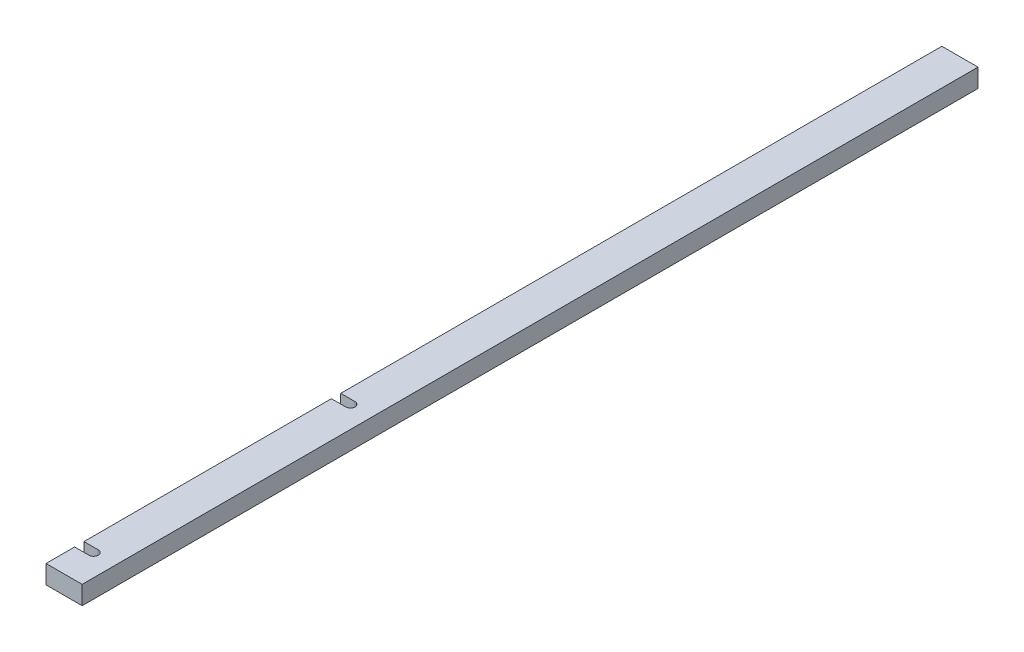
SolidWorks part; units mm, degrees
ref_plane "Front Plane" through (0, 0, 0) normal (0, 0, 1) x (1, 0, 0)
ref_plane "Top Plane" through (0, 0, 0) normal (0, 1, 0) x (1, 0, 0)
ref_plane "Right Plane" through (0, 0, 0) normal (1, 0, 0) x (0, 0, -1)
sketch "Sketch1" plane through (0, 0, 0) normal (0, 0, 1) x (1, 0, 0)
  line L1 (-26.0809, 10.1006) -> (11.9191, 10.1006)
  line L2 (-26.0809, 10.1006) -> (-26.0809, -9.3994)
  line L3 (-26.0809, -9.3994) -> (11.9191, -9.3994)
  line L4 (11.9191, 10.1006) -> (11.9191, -9.3994)
  dimension "D1" = 19.5
  dimension "D2" = 38
extrude "Boss-Extrude1" add sketch "Sketch1" along normal blind 942
sketch "Sketch2" plane through (0, -9.3994, 0) normal (0, -1, 0) x (1, 0, 0)
  line L0 (-11.0809, 911.9) -> (-32.6439, 911.9)
  line L1 (-32.6439, 911.9) -> (-32.6439, 902.1)
  line L2 (-32.6439, 902.1) -> (-11.0809, 902.1)
  line L3 (-11.0809, 641.9) -> (-28.707, 641.9)
  line L4 (-28.707, 641.9) -> (-28.707, 632.1)
  line L5 (-28.707, 632.1) -> (-11.0809, 632.1)
  arc A0 (-11.0809, 902.1) -> (-11.0809, 911.9) centre (-11.0809, 907) ccw
  arc A1 (-11.0809, 632.1) -> (-11.0809, 641.9) centre (-11.0809, 637) ccw
  dimension "D1" = 4.9
extrude "Cut-Extrude1" cut sketch "Sketch2" against normal blind 61
